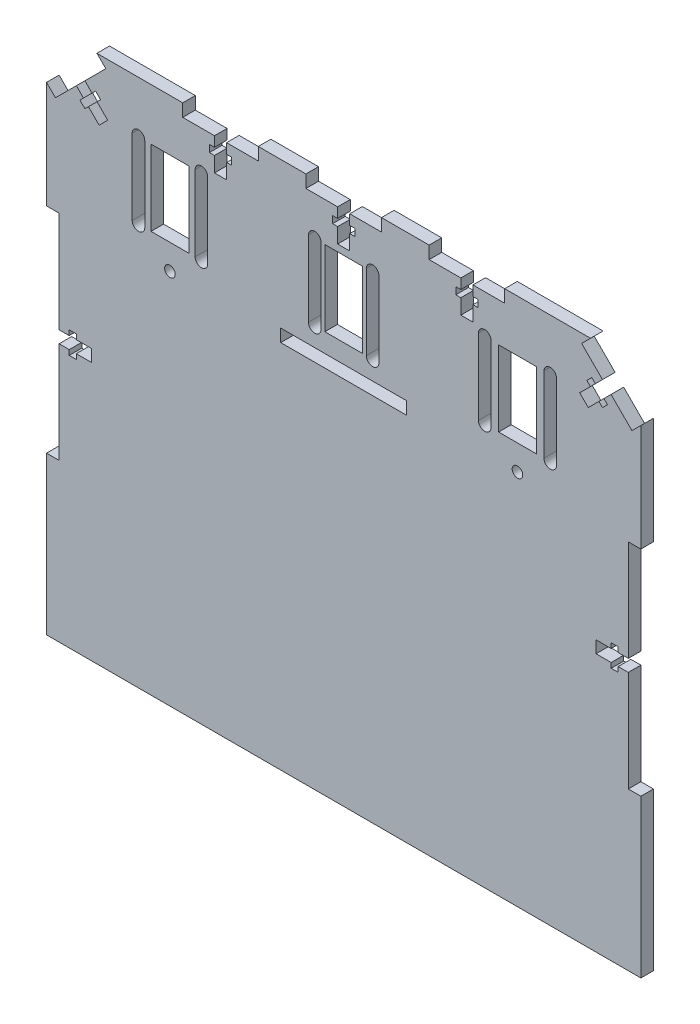
SolidWorks part; units mm, degrees
ref_plane "Front Plane" through (0, 0, 0) normal (0, 0, 1) x (1, 0, 0)
ref_plane "Top Plane" through (0, 0, 0) normal (0, 1, 0) x (1, 0, 0)
ref_plane "Right Plane" through (0, 0, 0) normal (1, 0, 0) x (0, 0, -1)
sketch "Sketch1" plane through (0, 0, 0) normal (0, 0, 1) x (1, 0, 0)
  line L0 (64.2262, -107) -> (118, -107)
  line L1 (-98, 103) -> (98, 103)
  line L3 (-118, -107) -> (-64.2262, -107)
  line L5 (-150, 100) -> (150, -100) construction
  line L6 (-150, -100) -> (150, 100) construction
  line L10 (0, 0) -> (0, 48.5738) construction
  line L12 (-47.5, 0) -> (47.5, 0) construction
  line L13 (47.5, -40) -> (47.5, 40) construction
  line L14 (47.5, 40) -> (78, 40) construction
  line L15 (78, 40) -> (78, -40) construction
  line L16 (78, -40) -> (47.5, -40) construction
  line L17 (-78, -40) -> (-47.5, -40) construction
  line L18 (-47.5, -40) -> (-47.5, 40) construction
  line L19 (-78, 40) -> (-78, -40) construction
  line L20 (-47.5, 40) -> (-78, 40) construction
  line L21 (78, 0) -> (118, 0) construction
  line L22 (118, 83) -> (118, -107)
  line L23 (-118, 83) -> (-118, -107)
  line L24 (-98, 103) -> (-98, 83) construction
  line L25 (-98, 83) -> (-118, 83) construction
  line L26 (0, 103) -> (0, -97) construction
  line L27 (-118, 83) -> (-98, 103)
  line L28 (98, 103) -> (118, 83)
  line L29 (-64.2262, -107) -> (64.2262, -107)
  point P0 (0, 0)
  point P19 (0, 0)
  point P22 (47.5, 0)
  point P33 (118, 0)
  dimension "D1" = 210
  dimension "D3" = 63
  dimension "D4" = 20
  dimension "D5" = 20
  dimension "D6" = 95
  dimension "D7" = 80
  dimension "D8" = 30.5
  dimension "D9" = 40
extrude "Boss-Extrude1" add sketch "Sketch1" along normal blind 5
sketch "Sketch4" plane through (0, 0, 5) normal (0, 0, 1) x (1, 0, 0)
  line L0 (-118, -2) -> (-113, -2) construction
  line L1 (-118, 83) -> (-118, -107) construction
  line L2 (-113, 40.5) -> (-113, -44.5)
  line L3 (-113, 40.5) -> (-118, 40.5)
  line L4 (-118, 40.5) -> (-118, -44.5)
  line L5 (-118, -44.5) -> (-113, -44.5)
  line L6 (0, 103) -> (0, 94.0884) construction
  line L7 (98, 103) -> (-98, 103) construction
  line L8 (118, -2) -> (113, -2) construction
  line L9 (118, -44.5) -> (113, -44.5)
  line L10 (118, 40.5) -> (118, -44.5)
  line L11 (113, 40.5) -> (118, 40.5)
  line L12 (113, 40.5) -> (113, -44.5)
  point P7 (-113, -2)
  point P20 (113, -2)
  dimension "D1" = 5
  dimension "D2" = 85
extrude "Cut-Extrude3" cut sketch "Sketch4" against normal through all
sketch "Sketch7" plane through (0, 0, 5) normal (0, 0, 1) x (1, 0, 0)
  line L0 (98, 103) -> (-98, 103) construction
  line L1 (-15, 98) -> (-2.4, 98)
  line L2 (-15, 98) -> (-15, 103)
  line L3 (-15, 103) -> (15, 103)
  line L4 (15, 98) -> (15, 103)
  line L5 (-15, 98) -> (15, 103) construction
  line L6 (-15, 103) -> (15, 98) construction
  line L7 (15, 98) -> (15, 103) construction
  line L8 (0, 98) -> (0, 79.0269) construction
  line L9 (2.4, 98) -> (2.4, 94)
  line L10 (2.4, 94) -> (4.4, 94)
  line L11 (4.4, 94) -> (4.4, 91.2)
  line L12 (4.4, 91.2) -> (2.4, 91.2)
  line L13 (2.4, 91.2) -> (2.4, 85.2)
  line L14 (-2.4, 91.2) -> (-2.4, 85.2)
  line L15 (-4.4, 91.2) -> (-2.4, 91.2)
  line L16 (-4.4, 94) -> (-4.4, 91.2)
  line L17 (-2.4, 94) -> (-4.4, 94)
  line L18 (-2.4, 98) -> (-2.4, 94)
  line L19 (-2.4, 85.2) -> (2.4, 85.2)
  line L20 (2.4, 98) -> (15, 98)
  line L21 (-63.9151, 98) -> (-33.9151, 98) construction
  line L22 (-48.9151, 80.824) -> (0, 80.824) construction
  line L23 (-24.4575, 80.824) -> (-24.4575, 85.2) construction
  line L24 (-48.9151, 98) -> (-48.9151, 80.824) construction
  line L25 (-33.9151, 103) -> (-63.9151, 98) construction
  line L42 (-33.9151, 98) -> (-63.9151, 103) construction
  line L43 (-51.3151, 98) -> (-63.9151, 98)
  line L60 (-118, 83) -> (-114.4614, 79.4675) construction
  line L61 (-117.997, 83.003) -> (-114.4614, 79.4675) construction
  line L62 (-114.4614, 79.4675) -> (-104.463, 89.466) construction
  line L63 (-104.463, 89.466) -> (-95.1873, 80.1903) construction
  line L64 (-102.7659, 91.163) -> (-99.9375, 88.3346)
  line L65 (-100.9274, 93.0015) -> (-102.978, 90.9509) construction
  line L66 (-99.9375, 88.3346) -> (-98.5233, 89.7488)
  line L67 (-98.5233, 89.7488) -> (-96.5434, 87.7689)
  line L68 (-96.5434, 87.7689) -> (-97.9576, 86.3547)
  line L69 (-97.9576, 86.3547) -> (-93.7149, 82.1121)
  line L70 (-101.3517, 82.9606) -> (-97.109, 78.718)
  line L71 (-102.7659, 81.5464) -> (-101.3517, 82.9606)
  line L72 (-104.7458, 83.5263) -> (-102.7659, 81.5464)
  line L73 (-103.3316, 84.9405) -> (-104.7458, 83.5263)
  line L74 (-106.16, 87.7689) -> (-103.3316, 84.9405)
  line L75 (-106.16, 87.7689) -> (-102.7659, 91.163)
  line L76 (-93.7149, 82.1121) -> (-97.109, 78.718)
  line L77 (104.463, 89.466) -> (95.1873, 80.1903) construction
  line L78 (93.7149, 82.1121) -> (97.109, 78.718)
  line L79 (106.16, 87.7689) -> (102.7659, 91.163)
  line L80 (106.16, 87.7689) -> (103.3316, 84.9405)
  line L81 (103.3316, 84.9405) -> (104.7458, 83.5263)
  line L82 (104.7458, 83.5263) -> (102.7659, 81.5464)
  line L83 (102.7659, 81.5464) -> (101.3517, 82.9606)
  line L84 (101.3517, 82.9606) -> (97.109, 78.718)
  line L85 (97.9576, 86.3547) -> (93.7149, 82.1121)
  line L86 (96.5434, 87.7689) -> (97.9576, 86.3547)
  line L87 (98.5233, 89.7488) -> (96.5434, 87.7689)
  line L88 (99.9375, 88.3346) -> (98.5233, 89.7488)
  line L89 (102.7659, 91.163) -> (99.9375, 88.3346)
  line L90 (-63.9151, 98) -> (-63.9151, 103)
  line L91 (-33.9151, 103) -> (-63.9151, 103)
  line L92 (-46.5151, 85.2) -> (-51.3151, 85.2)
  line L93 (-46.5151, 98) -> (-46.5151, 94)
  line L94 (-46.5151, 94) -> (-44.5151, 94)
  line L95 (-44.5151, 94) -> (-44.5151, 91.2)
  line L96 (-44.5151, 91.2) -> (-46.5151, 91.2)
  line L97 (-46.5151, 91.2) -> (-46.5151, 85.2)
  line L98 (-51.3151, 91.2) -> (-51.3151, 85.2)
  line L99 (-53.3151, 91.2) -> (-51.3151, 91.2)
  line L100 (-53.3151, 94) -> (-53.3151, 91.2)
  line L101 (-51.3151, 94) -> (-53.3151, 94)
  line L102 (-51.3151, 98) -> (-51.3151, 94)
  line L103 (-33.9151, 98) -> (-33.9151, 103)
  line L104 (-33.9151, 98) -> (-46.5151, 98)
  line L105 (33.9151, 98) -> (63.9151, 103) construction
  line L106 (33.9151, 103) -> (63.9151, 98) construction
  line L107 (63.9151, 98) -> (33.9151, 98) construction
  line L108 (33.9151, 98) -> (46.5151, 98)
  line L109 (33.9151, 98) -> (33.9151, 103)
  line L110 (51.3151, 98) -> (51.3151, 94)
  line L111 (51.3151, 94) -> (53.3151, 94)
  line L112 (53.3151, 94) -> (53.3151, 91.2)
  line L113 (53.3151, 91.2) -> (51.3151, 91.2)
  line L114 (51.3151, 91.2) -> (51.3151, 85.2)
  line L115 (46.5151, 91.2) -> (46.5151, 85.2)
  line L116 (44.5151, 91.2) -> (46.5151, 91.2)
  line L117 (44.5151, 94) -> (44.5151, 91.2)
  line L118 (46.5151, 94) -> (44.5151, 94)
  line L119 (46.5151, 98) -> (46.5151, 94)
  line L120 (46.5151, 85.2) -> (51.3151, 85.2)
  line L121 (33.9151, 103) -> (63.9151, 103)
  line L122 (63.9151, 98) -> (63.9151, 103)
  line L123 (51.3151, 98) -> (63.9151, 98)
  point P4 (0, 100.5)
  point P47 (-48.9151, 100.5)
  point P64 (48.9151, 100.5)
  dimension "D1" = 2.4
  dimension "D2" = 4
  dimension "D3" = 2.8
  dimension "D4" = 2
  dimension "D5" = 6
  dimension "D6" = 2.4
  dimension "D7" = 4
  dimension "D8" = 2.8
  dimension "D9" = 2
  dimension "D10" = 6
  dimension "D11" = 2.4
  dimension "D12" = 2.4
extrude "Cut-Extrude6" cut sketch "Sketch7" against normal through all
sketch "Sketch9" plane through (0, 0, 5) normal (0, 0, 1) x (1, 0, 0)
  line L0 (94.4675, 99.4614) -> (98, 103)
  line L1 (98, 103) -> (118, 83)
  line L2 (118, 83) -> (114.4645, 79.4645)
  line L3 (114.4645, 79.4645) -> (94.4675, 99.4614)
  line L4 (-118, 83) -> (-114.4614, 79.4675)
  line L5 (-114.4614, 79.4675) -> (-94.4645, 99.4645)
  line L6 (-94.4645, 99.4645) -> (-98, 103)
  line L7 (-98, 103) -> (-118, 83)
extrude "Cut-Extrude8" cut sketch "Sketch9" against normal blind 5
sketch "Sketch10" plane through (0, 0, 5) normal (0, 0, 1) x (1, 0, 0)
  line L0 (25, 45) -> (-25, 45) construction
  line L1 (-25, 40) -> (25, 40)
  line L2 (-25, 40) -> (-25, 45)
  line L3 (-25, 45) -> (25, 45)
  line L4 (25, 40) -> (25, 45)
  line L5 (-25, 40) -> (25, 45) construction
  line L6 (-25, 45) -> (25, 40) construction
  line L7 (25, 42.5) -> (113, 42.5) construction
  line L8 (113, 40.5) -> (113, 53.75) construction
  line L9 (0, 45) -> (0, 67.5) construction
  line L10 (-69, 42.5) -> (-69, 67.5) construction
  line L11 (69, 42.5) -> (69, 67.5) construction
  line L12 (-61.5, 67.5) -> (-56.5, 67.5) construction
  line L13 (-76.5, 82.5) -> (-61.5, 82.5)
  line L14 (-76.5, 82.5) -> (-76.5, 52.5)
  line L15 (-76.5, 52.5) -> (-61.5, 52.5)
  line L16 (-61.5, 82.5) -> (-61.5, 52.5)
  line L17 (-76.5, 82.5) -> (-61.5, 52.5) construction
  line L18 (-76.5, 52.5) -> (-61.5, 82.5) construction
  line L19 (7.5, 82.5) -> (-7.5, 82.5)
  line L20 (7.5, 82.5) -> (7.5, 52.5)
  line L21 (7.5, 52.5) -> (-7.5, 52.5)
  line L22 (-7.5, 82.5) -> (-7.5, 52.5)
  line L23 (7.5, 82.5) -> (-7.5, 52.5) construction
  line L24 (7.5, 52.5) -> (-7.5, 82.5) construction
  line L25 (61.5, 82.5) -> (76.5, 82.5)
  line L26 (61.5, 82.5) -> (61.5, 52.5)
  line L27 (61.5, 52.5) -> (76.5, 52.5)
  line L28 (76.5, 82.5) -> (76.5, 52.5)
  line L29 (61.5, 82.5) -> (76.5, 52.5) construction
  line L30 (61.5, 52.5) -> (76.5, 82.5) construction
  line L31 (-56.5, 82.5) -> (-56.5, 52.5) construction
  line L32 (-54, 82.5) -> (-54, 52.5)
  line L33 (-59, 82.5) -> (-59, 52.5)
  line L34 (-11.5, 82.5) -> (-11.5, 52.5) construction
  line L35 (-9, 82.5) -> (-9, 52.5)
  line L36 (-14, 82.5) -> (-14, 52.5)
  line L37 (56, 82.5) -> (56, 52.5) construction
  line L38 (58.5, 82.5) -> (58.5, 52.5)
  line L39 (53.5, 82.5) -> (53.5, 52.5)
  line L40 (-81.5, 82.5) -> (-81.5, 52.5) construction
  line L41 (-84, 82.5) -> (-84, 52.5)
  line L42 (-79, 82.5) -> (-79, 52.5)
  line L43 (11.5, 82.5) -> (11.5, 52.5) construction
  line L44 (9, 82.5) -> (9, 52.5)
  line L45 (14, 82.5) -> (14, 52.5)
  line L46 (82, 82.5) -> (82, 52.5) construction
  line L47 (79.5, 82.5) -> (79.5, 52.5)
  line L48 (84.5, 82.5) -> (84.5, 52.5)
  circle A0 centre (69, 42.5) radius 2.1
  circle A1 centre (-69, 42.5) radius 2.1
  arc A2 (-54, 82.5) -> (-59, 82.5) centre (-56.5, 82.5) ccw
  arc A3 (-59, 52.5) -> (-54, 52.5) centre (-56.5, 52.5) ccw
  arc A4 (-9, 82.5) -> (-14, 82.5) centre (-11.5, 82.5) ccw
  arc A5 (-14, 52.5) -> (-9, 52.5) centre (-11.5, 52.5) ccw
  arc A6 (58.5, 82.5) -> (53.5, 82.5) centre (56, 82.5) ccw
  arc A7 (53.5, 52.5) -> (58.5, 52.5) centre (56, 52.5) ccw
  arc A8 (-84, 82.5) -> (-79, 82.5) centre (-81.5, 82.5) cw
  arc A9 (-79, 52.5) -> (-84, 52.5) centre (-81.5, 52.5) cw
  arc A10 (9, 82.5) -> (14, 82.5) centre (11.5, 82.5) cw
  arc A11 (14, 52.5) -> (9, 52.5) centre (11.5, 52.5) cw
  arc A12 (79.5, 82.5) -> (84.5, 82.5) centre (82, 82.5) cw
  arc A13 (84.5, 52.5) -> (79.5, 52.5) centre (82, 52.5) cw
  point P4 (0, 42.5)
  point P38 (-56.5, 67.5)
  point P46 (-11.5, 67.5)
  point P53 (56, 67.5)
  point P59 (-81.5, 67.5)
  point P66 (11.5, 67.5)
  point P73 (82, 67.5)
  dimension "D1" = 4.2
  dimension "D2" = 25
  dimension "D3" = 25
  dimension "D4" = 22.5
  dimension "D5" = 15
  dimension "D6" = 30
  dimension "D7" = 15
  dimension "D8" = 15
  dimension "D9" = 5
  dimension "D10" = 5
  dimension "D11" = 2
  dimension "D12" = 2
extrude "Cut-Extrude9" cut sketch "Sketch10" against normal blind 10
sketch "Sketch11" plane through (0, 0, 5) normal (0, 0, 1) x (1, 0, 0)
  line L0 (-113, -2) -> (-70.9466, -2) construction
  line L1 (-113, -44.5) -> (-113, 40.5) construction
  line L2 (-113, 0.4) -> (-109, 0.4)
  line L3 (-113, -44.5) -> (-113, 40.5) construction
  line L4 (-109, 0.4) -> (-109, 2.4)
  line L5 (-109, 2.4) -> (-106.2, 2.4)
  line L6 (-106.2, 2.4) -> (-106.2, 0.4)
  line L7 (-106.2, 0.4) -> (-100.2, 0.4)
  line L8 (-106.2, -4.4) -> (-100.2, -4.4)
  line L9 (-106.2, -6.4) -> (-106.2, -4.4)
  line L10 (-109, -6.4) -> (-106.2, -6.4)
  line L11 (-109, -4.4) -> (-109, -6.4)
  line L12 (-113, -4.4) -> (-109, -4.4)
  line L13 (-100.2, -4.4) -> (-100.2, 0.4)
  line L14 (-113, 0.4) -> (-113, -4.4)
  line L15 (0, -107) -> (0, -79.7189) construction
  line L16 (-118, -107) -> (118, -107) construction
  line L17 (113, 0.4) -> (113, -4.4)
  line L18 (100.2, -4.4) -> (100.2, 0.4)
  line L19 (113, -4.4) -> (109, -4.4)
  line L20 (109, -4.4) -> (109, -6.4)
  line L21 (109, -6.4) -> (106.2, -6.4)
  line L22 (106.2, -6.4) -> (106.2, -4.4)
  line L23 (106.2, -4.4) -> (100.2, -4.4)
  line L24 (106.2, 0.4) -> (100.2, 0.4)
  line L25 (106.2, 2.4) -> (106.2, 0.4)
  line L26 (109, 2.4) -> (106.2, 2.4)
  line L27 (109, 0.4) -> (109, 2.4)
  line L28 (113, 0.4) -> (109, 0.4)
  dimension "D1" = 2.4
  dimension "D2" = 4
  dimension "D3" = 2.8
  dimension "D4" = 2
  dimension "D5" = 6
  dimension "D6" = 2.4
extrude "Cut-Extrude10" cut sketch "Sketch11" against normal blind 10
